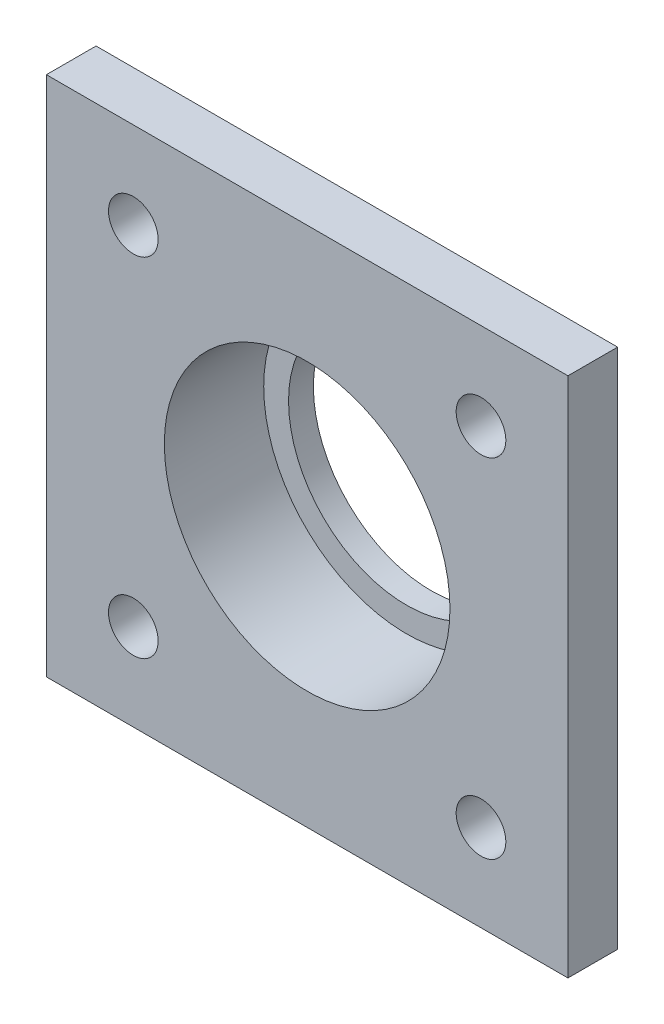
SolidWorks part; units mm, degrees
material "AISI 316 Annealed Stainless Steel Bar (SS)"
ref_plane "Front Plane" through (0, 0, 0) normal (0, 0, 1) x (1, 0, 0)
ref_plane "Top Plane" through (0, 0, 0) normal (0, 1, 0) x (1, 0, 0)
ref_plane "Right Plane" through (0, 0, 0) normal (1, 0, 0) x (0, 0, -1)
sketch "Sketch1" plane through (0, 0, 0) normal (0, 0, 1) x (1, 0, 0)
  line L1 (-21, -21) -> (21, -21)
  line L2 (-21, -21) -> (-21, 21)
  line L3 (-21, 21) -> (21, 21)
  line L4 (21, -21) -> (21, 21)
  line L5 (-21, -21) -> (21, 21) construction
  line L6 (-21, 21) -> (21, -21) construction
  circle A0 centre (0, 0) radius 11.5
  circle A1 centre (-14, 14) radius 2
  circle A2 centre (14, 14) radius 2
  circle A3 centre (14, -14) radius 2
  circle A4 centre (-14, -14) radius 2
  point P0 (0, 0)
  point P19 (0, 0)
  dimension "D1" = 23
  dimension "D2" = 4
  dimension "D5" = 19.799
  dimension "D6" = 4
  dimension "D3" = 42
  dimension "D4" = 42
extrude "Boss-Extrude1" add sketch "Sketch1" along normal blind 4 contours A4 L2 L1 L4 A2 L3 A3 A1 A0
sketch "Sketch2" plane through (0, 0, 0) normal (0, 0, 1) x (1, 0, 0)
  circle A0 centre (0, 0) radius 15
  circle A1 centre (0, 0) radius 11.5
  dimension "D1" = 30
  dimension "D2" = 23
extrude "Boss-Extrude2" add sketch "Sketch2" against normal blind 6
sketch "Sketch3" plane through (0, 0, -6) normal (0, 0, -1) x (-1, 0, 0)
  circle A0 centre (0, 0) radius 11.5
  circle A1 centre (0, 0) radius 9.5
  dimension "D1" = 23
  dimension "D2" = 19
extrude "Boss-Extrude3" add sketch "Sketch3" against normal blind 2
fillet "Fillet1" radius 2 1 edges at (15, 0, 0)
